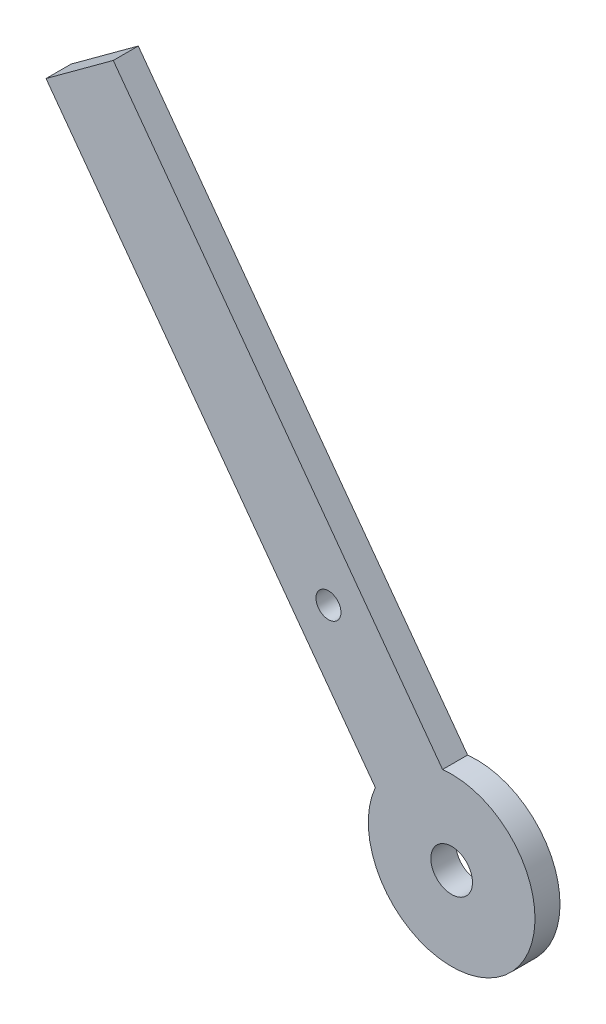
SolidWorks part; units mm, degrees
ref_plane "Front Plane" through (0, 0, 0) normal (0, 0, 1) x (1, 0, 0)
ref_plane "Top Plane" through (0, 0, 0) normal (0, 1, 0) x (1, 0, 0)
ref_plane "Right Plane" through (0, 0, 0) normal (1, 0, 0) x (0, 0, -1)
sketch "Sketch1" plane through (0, 0, 0) normal (0, 0, 1) x (1, 0, 0)
  line L2 (-91.8444, -12.0463) -> (-12.0463, 91.8444) construction
  line L4 (210.311, -244.1307) -> (290.109, -140.24) construction
  line L8 (-91.8444, -12.0463) -> (210.311, -244.1307) construction
  line L13 (8.261, 114.776) -> (4.228, 111.8204)
  line L14 (4.228, 111.8204) -> (43.7379, 57.9082)
  line L15 (52.89, 53.8786) -> (8.261, 114.776) construction
  line L16 (-12.0463, 91.8444) -> (290.109, -140.24) construction
  line L17 (-13.8738, 89.4652) -> (288.2816, -142.6192) construction
  line L18 (-90.0169, -9.6671) -> (212.1384, -241.7515) construction
  line L19 (8.261, 114.776) -> (12.2939, 117.7316)
  line L20 (12.2939, 117.7316) -> (51.8037, 63.8194)
  line L21 (110.6269, -163.7809) -> (186.7701, -64.6486) construction
  line L22 (49.5662, -38.0716) -> (148.6985, -114.2147) construction
  line L23 (11.4946, -87.6377) -> (87.6377, 11.4946) construction
  line L24 (-59.8659, -65.0275) -> (65.0275, -59.8659) construction
  line L25 (-51.3774, -270.4192) -> (-65.1764, 63.4689) construction
  line L26 (73.7293, -270.4192) -> (59.7668, 67.4254) construction
  line L27 (-54.3799, -270.4192) -> (-68.1739, 63.345) construction
  line L28 (76.7319, -270.4192) -> (62.7642, 67.5493) construction
  line L29 (-54.3799, -270.4192) -> (-20.9597, -270.4192) construction
  line L30 (-20.9597, -270.4192) -> (73.7293, -270.4192) construction
  line L31 (73.7293, -270.4192) -> (76.7319, -270.4192) construction
  line L32 (-68.1739, 63.345) -> (-65.1764, 63.4689) construction
  line L33 (-65.1764, 63.4689) -> (59.7668, 67.4254) construction
  line L34 (59.7668, 67.4254) -> (62.7642, 67.5493) construction
  line L36 (205.0733, -91.6138) -> (236.6815, -91.6138) construction
  line L37 (113.0061, -165.6083) -> (189.1493, -66.476) construction
  circle A18 centre (0, 0) radius 62.5 construction
  circle A19 centre (200.6438, -154.1138) radius 62.5 construction
  circle A20 centre (0, 0) radius 65.5 construction
  circle A21 centre (99.1323, -76.1432) radius 62.5 construction
  circle A22 centre (52.89, 53.8786) radius 75.5 construction
  circle A23 centre (52.89, 53.8786) radius 2.5
  circle A24 centre (38.1122, 74.0433) radius 1.5
  arc A25 (43.7379, 57.9082) -> (51.8037, 63.8194) centre (52.89, 53.8786) ccw
  point P42 (131.2629, -30.8403)
  dimension "D1" = 125
  dimension "D2" = 125
  dimension "D3" = 5
  dimension "D4" = 5
  dimension "D5" = 25
  dimension "D6" = 3
  dimension "D10" = 3
  dimension "D8" = 5
  dimension "D9" = 125
  dimension "D11" = 3
  dimension "D12" = 10
  dimension "D7" = 10
extrude "Boss-Extrude1" add sketch "Sketch1" along normal blind 3
